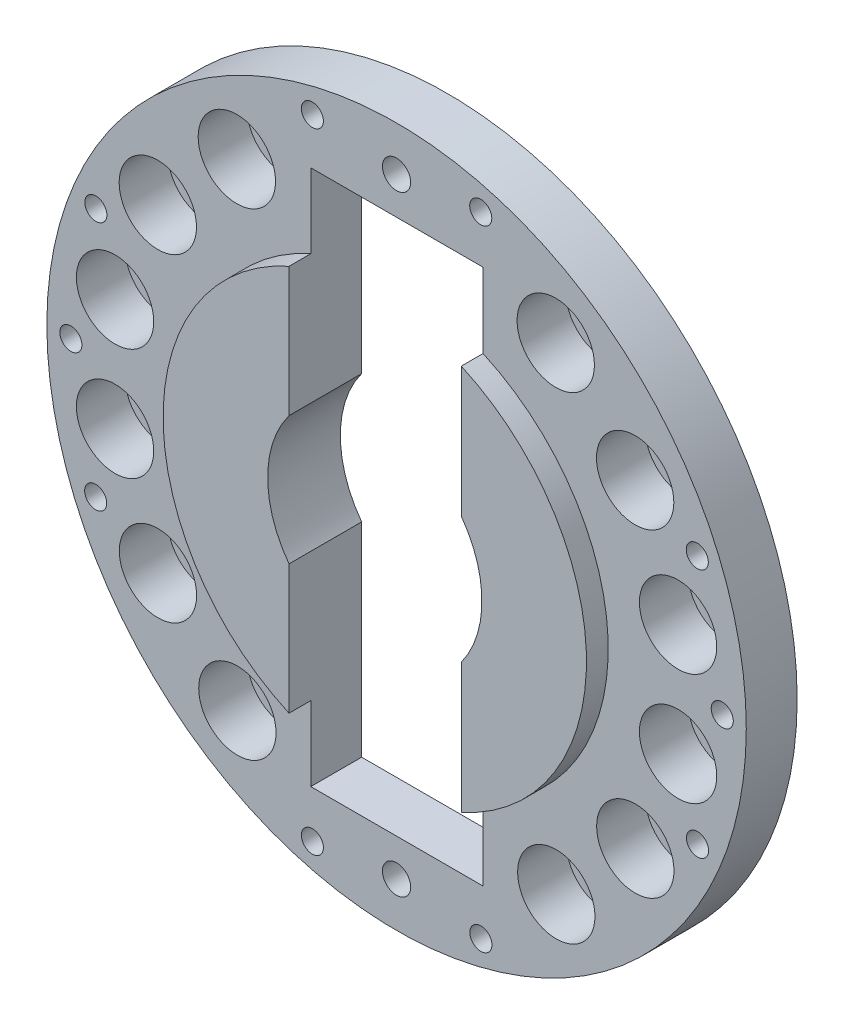
SolidWorks part; units mm, degrees
material "Alloy Steel"
ref_plane "Front Plane" through (0, 0, 0) normal (0, 0, 1) x (1, 0, 0)
ref_plane "Top Plane" through (0, 0, 0) normal (0, 1, 0) x (1, 0, 0)
ref_plane "Right Plane" through (0, 0, 0) normal (1, 0, 0) x (0, 0, -1)
sketch "Sketch1" plane through (0, 0, 0) normal (0, 0, 1) x (1, 0, 0)
  line L0 (0, -272.7935) -> (0, 272.7935) construction
  line L1 (-272.7935, 0) -> (272.7935, 0) construction
  line L2 (-252.0553, 104.3284) -> (252.0553, -104.3284) construction
  line L3 (70.6327, -263.4906) -> (-70.6327, 263.4906) construction
  line L4 (-252.0048, -104.4503) -> (252.0048, 104.4503) construction
  line L5 (-70.5135, -263.5225) -> (70.5135, 263.5225) construction
  line L6 (-249.1679, -49.5567) -> (249.1679, 49.5567) construction
  line L7 (-211.177, -141.2261) -> (211.177, 141.2261) construction
  line L8 (-140.8875, -211.403) -> (140.8875, 211.403) construction
  line L9 (141.3731, -211.0786) -> (-141.3731, 211.0786) construction
  line L10 (211.3088, -141.0288) -> (-211.3088, 141.0288) construction
  line L11 (267.5437, -53.26) -> (-267.5437, 53.26) construction
  circle A0 centre (0, 0) radius 272.7935
  circle A2 centre (0, 0) radius 164.4498
  circle A3 centre (0, 0) radius 83.5635
  circle A4 centre (0, 238.0005) radius 11.0096
  circle A5 centre (0, -238.0005) radius 11.0096
  circle A7 centre (-254.0483, 0) radius 8.6176
  circle A8 centre (254.0483, 0) radius 8.6176
  circle A9 centre (234.565, 97.5695) radius 8.6176
  circle A10 centre (65.6682, 245.4144) radius 8.6176
  circle A11 centre (-65.6682, 245.4144) radius 8.6176
  circle A12 centre (-234.565, 97.5695) radius 8.6176
  circle A13 centre (234.7351, -97.1594) radius 8.6176
  circle A14 centre (65.7791, -245.3847) radius 8.6176
  circle A15 centre (-65.6682, -245.4144) radius 8.6176
  circle A16 centre (-234.6881, -97.2729) radius 8.6176
  circle A19 centre (-219.5848, -43.673) radius 30.1625
  circle A20 centre (219.5848, 43.673) radius 30.1625
  circle A21 centre (186.1045, 124.4587) radius 30.1625
  circle A22 centre (-186.1045, -124.4587) radius 30.1625
  circle A23 centre (124.1603, 186.3036) radius 30.1625
  circle A24 centre (-124.1603, -186.3036) radius 30.1625
  circle A25 centre (-124.5882, 186.0178) radius 30.1625
  circle A26 centre (124.5882, -186.0178) radius 30.1625
  circle A27 centre (-186.2206, 124.2848) radius 30.1625
  circle A28 centre (186.2206, -124.2848) radius 30.1625
  circle A29 centre (-219.5772, 43.7113) radius 30.1625
  circle A30 centre (219.5848, -43.673) radius 30.1625
extrude "Extrude5" add sketch "Sketch1" along normal blind 39.6926 contours A0 A30 A29 A28 A27 A26 A25 A24 A23 A22 A21 A20 A19 A16 A15 A14 A13 A12 A11 A10 A9 A8 A7 A5 A4 A2 | A2 A3
sketch "Sketch3" plane through (0, 0, 39.6926) normal (0, 0, 1) x (1, 0, 0)
  line L0 (-66.9036, 150.9507) -> (-66.9036, 50.0676)
  line L1 (67.4497, -150.7075) -> (67.4497, -49.3294) construction
  line L2 (-66.9036, 50.0676) -> (-66.9036, 150.9507) construction
  line L3 (67.4497, 150.7075) -> (67.4497, 49.3294)
  line L4 (-66.9036, -150.9507) -> (-66.9036, -50.0676)
  line L6 (67.4497, -150.7075) -> (67.4497, -49.3294)
  arc A0 (-66.9036, 150.9507) -> (-66.9036, -150.9507) centre (0, 0) ccw
  arc A1 (-66.9036, 50.0676) -> (-66.9036, -50.0676) centre (0, 0) ccw
  arc A2 (67.4497, -49.3294) -> (67.4497, 49.3294) centre (0, 0) ccw
  arc A3 (67.4497, -150.7075) -> (67.4497, 150.7075) centre (0, 0) ccw
extrude "Extrude8" add sketch "Sketch3" along normal blind 16.9748
sketch "Sketch4" plane through (0, 0, 56.6674) normal (0, 0, 1) x (1, 0, 0)
  line L3 (67.4497, 209.0077) -> (-66.9036, 209.0077)
  line L4 (67.4497, -209.0077) -> (-66.9036, -209.0077)
  line L7 (-66.9036, 209.0077) -> (-66.9036, -209.0077)
  line L8 (67.4497, 209.0077) -> (67.4497, -209.0077)
extrude "Extrude10" cut sketch "Sketch4" against normal blind 64.8322
sketch "Sketch7" plane through (0, 0, 0) normal (0, 0, -1) x (-1, 0, 0)
  circle A0 centre (-124.1603, 186.3036) radius 30.1625
  circle A2 centre (-186.1045, 124.4587) radius 30.1625
  circle A4 centre (-219.5848, 43.673) radius 30.1625
  circle A6 centre (-219.5848, -43.673) radius 30.1625
  circle A8 centre (-186.2206, -124.2848) radius 30.1625
  circle A10 centre (-124.5882, -186.0178) radius 30.1625
  circle A12 centre (124.1603, -186.3036) radius 30.1625
  circle A14 centre (186.1045, -124.4587) radius 30.1625
  circle A16 centre (219.5848, -43.673) radius 30.1625
  circle A18 centre (219.5772, 43.7113) radius 30.1625
  circle A20 centre (186.2206, 124.2848) radius 30.1625
  circle A21 centre (186.2206, 124.2848) radius 111125
  circle A23 centre (124.5882, 186.0178) radius 30.1625
extrude "Extrude12" add sketch "Sketch7" against normal blind 1.5926
hole_wizard "1-8 Tapped Hole1" positions "3DSketch1" profile "Sketch10" tap size "1-8" standard "Ansi Inch" end condition through all
sketch3d "3DSketch1"
  line L0 (124.1603, 186.3036, 39.6926) -> (124.1603, 186.3036, 1.5926) construction
  line L1 (186.1045, 124.4587, 39.6926) -> (186.1045, 124.4587, 1.5926) construction
  line L2 (219.5848, 43.673, 39.6926) -> (219.5848, 43.673, 1.5926) construction
  line L3 (219.5848, -43.673, 39.6926) -> (219.5848, -43.673, 1.5926) construction
  line L4 (186.2206, -124.2848, 39.6926) -> (186.2206, -124.2848, 1.5926) construction
  line L5 (124.5882, -186.0178, 39.6926) -> (124.5882, -186.0178, 1.5926) construction
  line L6 (-124.1603, -186.3036, 39.6926) -> (-124.1603, -186.3036, 1.5926) construction
  line L7 (-186.1045, -124.4587, 39.6926) -> (-186.1045, -124.4587, 1.5926) construction
  line L8 (-219.5848, -43.673, 39.6926) -> (-219.5848, -43.673, 1.5926) construction
  line L9 (-219.5772, 43.7113, 39.6926) -> (-219.5772, 43.7113, 1.5926) construction
  line L10 (-186.2206, 124.2848, 39.6926) -> (-186.2206, 124.2848, 1.5926) construction
  line L11 (-124.5882, 186.0178, 39.6926) -> (-124.5882, 186.0178, 1.5926) construction
  point P1 (124.1603, 186.3036, 39.6926)
  point P5 (124.1603, 186.3036, 1.5926)
  point P7 (186.1045, 124.4587, 1.5926)
  point P11 (219.5848, 43.673, 39.6926)
  point P15 (219.5848, -43.673, 39.6926)
  point P19 (186.2206, -124.2848, 39.6926)
  point P23 (124.5882, -186.0178, 39.6926)
  point P27 (-124.1603, -186.3036, 1.5926)
  point P31 (-186.1045, -124.4587, 39.6926)
  point P35 (-219.5848, -43.673, 1.5926)
  point P39 (-219.5772, 43.7113, 1.5926)
  point P43 (-186.2206, 124.2848, 39.6926)
  point P47 (-124.5882, 186.0178, 1.5926)
sketch "Sketch10" plane through (124.1603, 186.3036, 39.6926) normal (1, 0, 0) x (0, -1, 0)
  line L0 (0, 0) -> (0, 39.6926)
  line L1 (0, 39.6926) -> (11.1125, 39.6926)
  line L2 (11.1125, 39.6926) -> (11.1125, 0)
  line L5 (11.1125, 0) -> (0, 0)
  line L11 (0, -6.35) -> (0, 107.95) construction
  dimension "Thru Tap Drill Dia." = 22.225
  dimension "Thru Tap Drill Depth" = 39.6926
cosmetic thread "Hole Thread1" parameters "D2"=25.4
cosmetic thread "Hole Thread2" parameters "D2"=25.4
cosmetic thread "Hole Thread3" parameters "D2"=25.4
cosmetic thread "Hole Thread4" parameters "D2"=25.4
cosmetic thread "Hole Thread5" parameters "D2"=25.4
cosmetic thread "Hole Thread6" parameters "D2"=25.4
cosmetic thread "Hole Thread7" parameters "D2"=25.4
cosmetic thread "Hole Thread8" parameters "D2"=25.4
cosmetic thread "Hole Thread9" parameters "D2"=25.4
cosmetic thread "Hole Thread10" parameters "D2"=25.4
cosmetic thread "Hole Thread11" parameters "D2"=25.4
cosmetic thread "Hole Thread12" parameters "D2"=25.4
cosmetic thread "Hole Thread13" parameters "D2"=25.4
